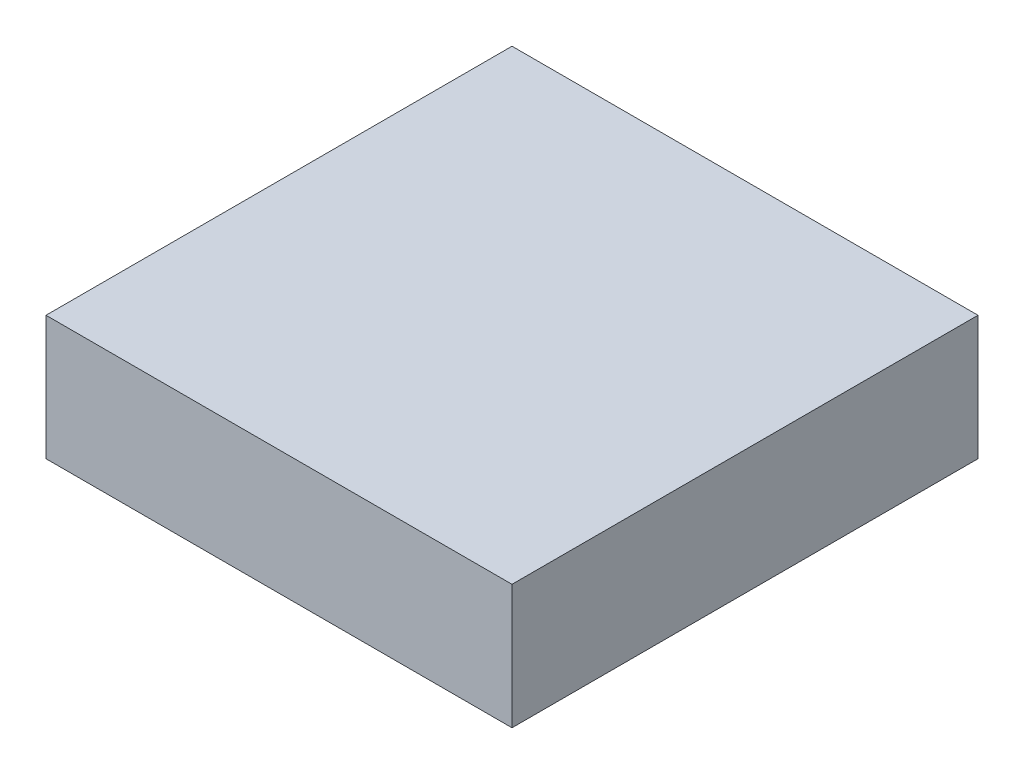
SolidWorks part; units mm, degrees
ref_plane "Front Plane" through (0, 0, 0) normal (0, 0, 1) x (1, 0, 0)
ref_plane "Top Plane" through (0, 0, 0) normal (0, 1, 0) x (1, 0, 0)
ref_plane "Right Plane" through (0, 0, 0) normal (1, 0, 0) x (0, 0, -1)
sketch "Sketch1" plane through (0, 0, 0) normal (0, 1, 0) x (1, 0, 0)
  line L1 (-102.2117, 48.8033) -> (-27.2117, 48.8033)
  line L2 (-102.2117, 48.8033) -> (-102.2117, -26.1967)
  line L3 (-102.2117, -26.1967) -> (-27.2117, -26.1967)
  line L4 (-27.2117, 48.8033) -> (-27.2117, -26.1967)
  dimension "D1" = 75
  dimension "D2" = 75
extrude "Boss-Extrude1" add sketch "Sketch1" along normal blind 20
